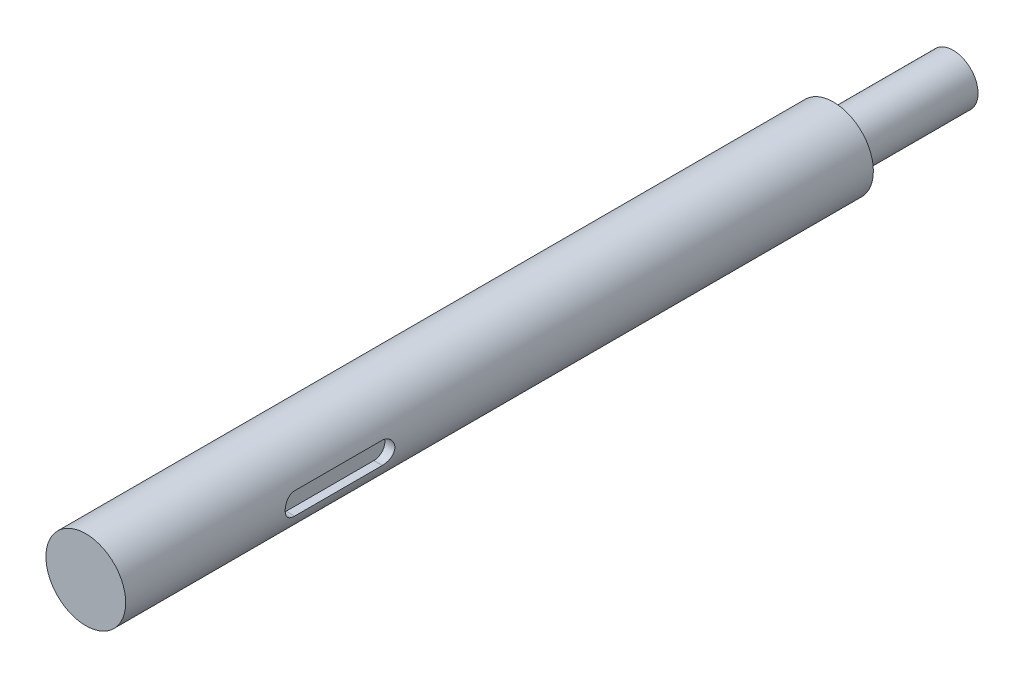
SolidWorks part; units mm, degrees
ref_plane "正面" through (0, 0, 0) normal (0, 0, 1) x (1, 0, 0)
ref_plane "平面" through (0, 0, 0) normal (0, 1, 0) x (1, 0, 0)
ref_plane "右側面" through (0, 0, 0) normal (1, 0, 0) x (0, 0, -1)
sketch "ｽｹｯﾁ1" plane through (0, 0, 0) normal (0, 0, 1) x (1, 0, 0)
  circle A0 centre (0, 0) radius 4
  dimension "D1" = 8
extrude "ﾎﾞｽ - 押し出し1" add sketch "ｽｹｯﾁ1" along normal blind 75
sketch "ｽｹｯﾁ2" plane through (0, 0, 0) normal (0, 0, -1) x (-1, 0, 0)
  circle A0 centre (0, 0) radius 2.5
  dimension "D1" = 5
extrude "ﾎﾞｽ - 押し出し2" add sketch "ｽｹｯﾁ2" along normal blind 12
ref_plane "平面1" through (3, 0, 0) normal (1, 0, 0) x (0, 0, -1)
sketch "ｽｹｯﾁ3" plane through (3, 0, 0) normal (1, 0, 0) x (0, 0, -1)
  line L0 (-57.9, 0) -> (-49.1, 0) construction
  line L1 (-57.9, 1.1) -> (-49.1, 1.1)
  line L2 (-57.9, -1.1) -> (-49.1, -1.1)
  line L3 (-75, 4) -> (-75, -4) construction
  arc A0 (-57.9, 1.1) -> (-57.9, -1.1) centre (-57.9, 0) ccw
  arc A1 (-49.1, -1.1) -> (-49.1, 1.1) centre (-49.1, 0) ccw
  point P3 (-53.5, 0)
  point P8 (-59, 0)
  point P11 (-48, 0)
  dimension "D3" = 1.1
  dimension "D1" = 16
  dimension "D2" = 11
extrude "ｶｯﾄ - 押し出し1" cut sketch "ｽｹｯﾁ3" along normal through all
